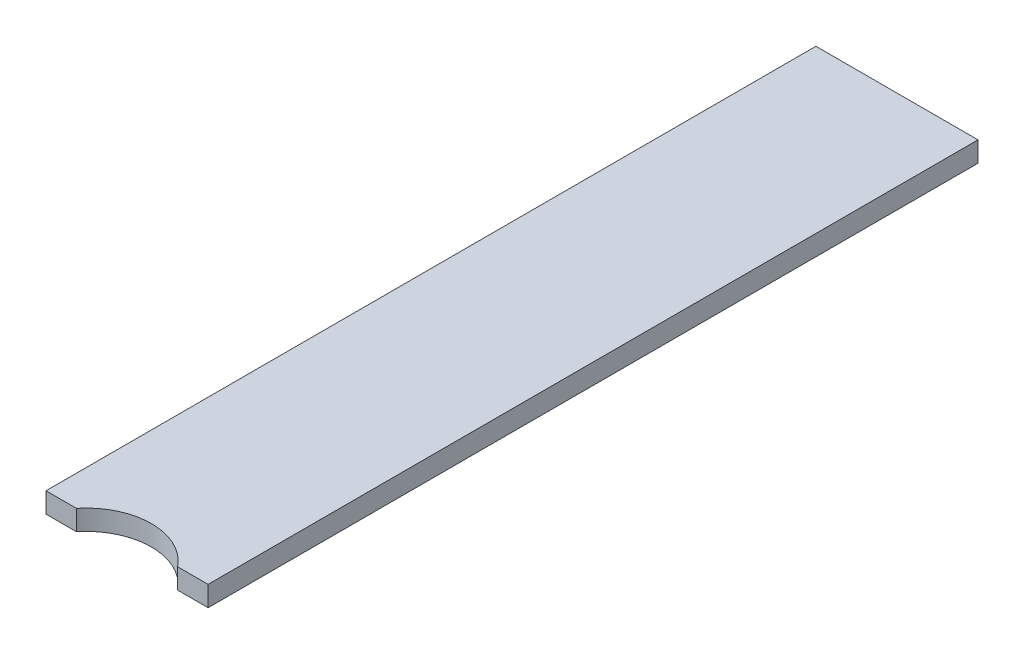
SolidWorks part; units mm, degrees
ref_plane "Спереди" through (0, 0, 0) normal (0, 0, 1) x (1, 0, 0)
ref_plane "Сверху" through (0, 0, 0) normal (0, 1, 0) x (1, 0, 0)
ref_plane "Справа" through (0, 0, 0) normal (1, 0, 0) x (0, 0, -1)
sketch "Эскиз1" plane through (0, 0, 0) normal (0, 0, 1) x (1, 0, 0)
  line L1 (0, 0) -> (40, 0)
  line L2 (0, 0) -> (0, -5)
  line L3 (0, -5) -> (40, -5)
  line L4 (40, 0) -> (40, -5)
  dimension "D1" = 5
  dimension "D2" = 40
extrude "Бобышка-Вытянуть1" add sketch "Эскиз1" along normal blind 200
sketch "Эскиз2" plane through (0, 0, 0) normal (0, 1, 0) x (1, 0, 0)
  line L0 (40, -200) -> (0, -200) construction
  circle A0 centre (20, -200) radius 16
  dimension "D1" = 32
extrude "Вырез-Вытянуть1" cut sketch "Эскиз2" against normal through all
sketch "Эскиз3" plane through (0, -5, 0) normal (0, -1, 0) x (1, 0, 0)
  line L0 (40, 200) -> (0, 200)
  line L1 (0, 200) -> (0, 190)
  line L2 (0, 200) -> (0, 0) construction
  line L3 (0, 190) -> (40, 190)
  line L4 (40, 200) -> (40, 0) construction
  line L5 (40, 190) -> (40, 200)
  dimension "D1" = 10
extrude "Вырез-Вытянуть2" cut sketch "Эскиз3" against normal through all
